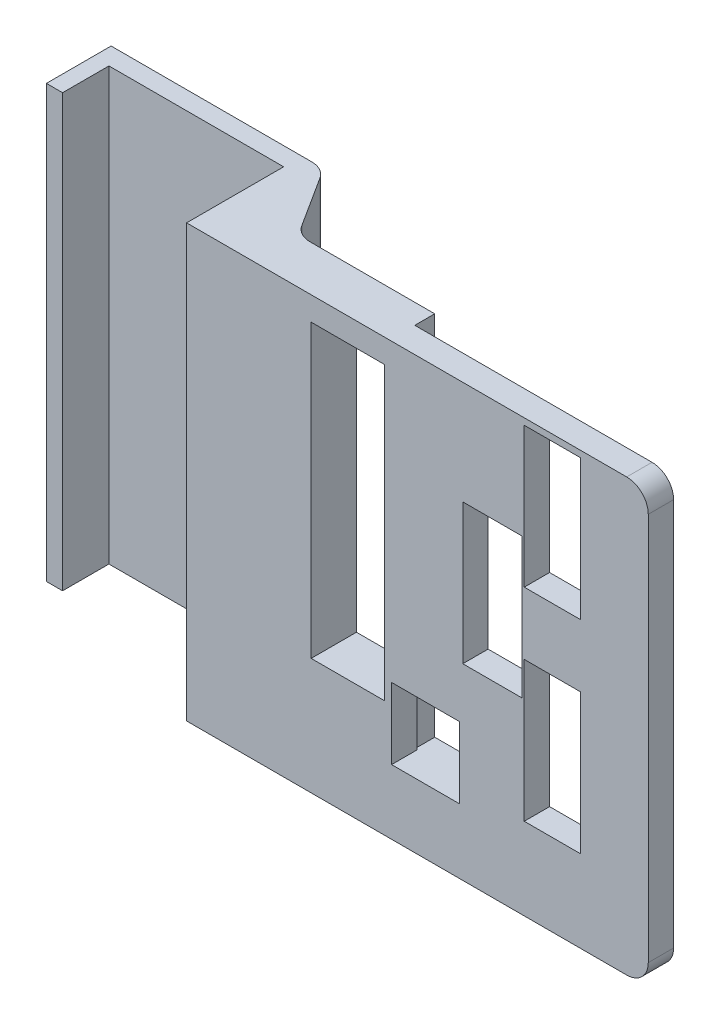
SolidWorks part; units mm, degrees
ref_plane "Front Plane" through (0, 0, 0) normal (0, 0, 1) x (1, 0, 0)
ref_plane "Top Plane" through (0, 0, 0) normal (0, 1, 0) x (1, 0, 0)
ref_plane "Right Plane" through (0, 0, 0) normal (1, 0, 0) x (0, 0, -1)
sketch "Sketch1" plane through (0, 0, 0) normal (0, 1, 0) x (1, 0, 0)
  line L0 (-38, -10.75) -> (-45.5, -10.75)
  line L1 (-38, -10.75) -> (38, -10.75) construction
  line L2 (-38, -10.75) -> (-38, 10.75) construction
  line L3 (-38, 10.75) -> (38, 10.75) construction
  line L4 (38, -10.75) -> (38, 10.75) construction
  line L5 (-38, -10.75) -> (38, 10.75) construction
  line L6 (-38, 10.75) -> (38, -10.75) construction
  line L7 (-45.5, -10.75) -> (-45.5, 19.25)
  line L8 (-45.5, 19.25) -> (53, 19.25)
  line L9 (53, 19.25) -> (73.75, -13.25)
  line L10 (73.75, -13.25) -> (137.04, -13.25)
  line L13 (43, -34.25) -> (43, 10.75)
  line L14 (43, 10.75) -> (-38, 10.75)
  line L15 (-38, 10.75) -> (-38, -10.75)
  line L16 (43, -34.25) -> (257.04, -34.25)
  line L19 (257.04, -34.25) -> (257.04, -22.5)
  line L20 (257.04, -22.5) -> (137.04, -22.5)
  line L21 (137.04, -22.5) -> (137.04, -13.25)
  point P0 (0, 0)
  point P12 (257.04, -31.7469)
  point P20 (140.6541, -13.1937)
  point P21 (131.5439, -3.7902)
  point P22 (249.881, -24.662)
  point P23 (144.1818, -29.0661)
  point P24 (256.75, -26.5768)
  point P25 (76.971, -13.25)
  point P26 (51.5036, 19.25)
  point P27 (49.3973, 19.25)
  point P28 (253.3277, -29.25)
  point P29 (0, 0)
  dimension "D1" = 76
  dimension "D2" = 21.5
  dimension "D3" = 7.5
  dimension "D4" = 30
  dimension "D5" = 5
  dimension "D6" = 24
  dimension "D7" = 30.75
  dimension "D8" = 63.29
  dimension "D9" = 9.25
  dimension "D10" = 120
  dimension "D11" = 45
  dimension "D12" = 10
extrude "Boss-Extrude1" add sketch "Sketch1" along normal blind 200
sketch "Sketch2" plane through (0, 0, 13.25) normal (0, 0, -1) x (-1, 0, 0)
  line L9 (-73.75, 200) -> (-73.75, 0) construction
  line L11 (-134.75, 189) -> (-100.75, 189)
  line L13 (-134.75, 189) -> (-134.75, 54)
  line L14 (-134.75, 54) -> (-100.75, 54)
  line L15 (-100.75, 189) -> (-100.75, 54)
  line L16 (-225.54, 197) -> (-199.54, 197)
  line L17 (-225.54, 197) -> (-225.54, 132)
  line L18 (-225.54, 132) -> (-199.54, 132)
  line L19 (-199.54, 197) -> (-199.54, 132)
  line L20 (-225.54, 103) -> (-199.54, 103)
  line L21 (-225.54, 103) -> (-225.54, 38)
  line L22 (-225.54, 38) -> (-199.54, 38)
  line L23 (-199.54, 103) -> (-199.54, 38)
  line L24 (-198.54, 152) -> (-171.04, 152)
  line L25 (-198.54, 152) -> (-198.54, 87)
  line L26 (-198.54, 87) -> (-171.04, 87)
  line L27 (-171.04, 152) -> (-171.04, 87)
  line L28 (-137.04, 200) -> (-73.75, 200) construction
  line L29 (-137.04, 200) -> (-137.04, 0) construction
  line L30 (-257.04, 200) -> (-137.04, 200) construction
  line L31 (-257.04, 0) -> (-137.04, 0) construction
  line L32 (-137.04, 200) -> (-137.04, 0) construction
  line L33 (-169.54, 63) -> (-138.04, 63)
  line L34 (-169.54, 63) -> (-169.54, 30)
  line L35 (-169.54, 30) -> (-138.04, 30)
  line L36 (-138.04, 63) -> (-138.04, 30)
  point P32 (-173.161, 63)
  dimension "D1" = 27
  dimension "D2" = 34
  dimension "D3" = 11
  dimension "D4" = 135
  dimension "D5" = 34
  dimension "D6" = 27.5
  dimension "D7" = 48
  dimension "D8" = 65
  dimension "D9" = 62.5
  dimension "D10" = 26
  dimension "D11" = 3
  dimension "D12" = 65
  dimension "D13" = 65
  dimension "D14" = 38
  dimension "D15" = 30
  dimension "D16" = 33
  dimension "D17" = 1
  dimension "D18" = 31.5
extrude "Cut-Extrude1" cut sketch "Sketch2" against normal blind 200
sketch "Sketch3" plane through (0, 0, 22.5) normal (0, 0, -1) x (-1, 0, 0)
  line L1 (-137.04, 0) -> (-169.54, 0)
  line L2 (-137.04, 0) -> (-137.04, 30)
  line L3 (-137.04, 30) -> (-169.54, 30)
  line L4 (-169.54, 0) -> (-169.54, 30)
extrude "Boss-Extrude2" add sketch "Sketch3" along normal up to surface (9.25 mm away) up to face at (117.75, 121.5, 13.25)
fillet "Fillet1" radius 10 4 edges at (53, 100, -19.25) (73.75, 100, 13.25) (257.04, 0, 28.375) (257.04, 200, 28.375)
